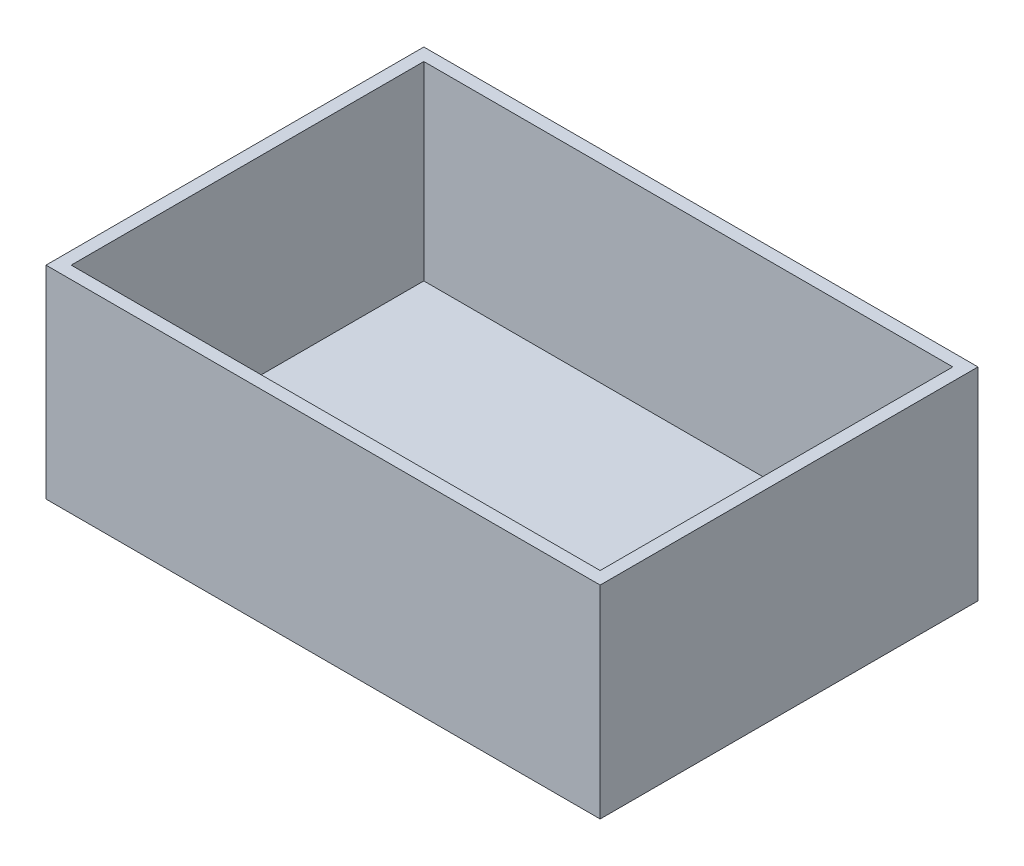
SolidWorks part; units mm, degrees
ref_plane "Front Plane" through (0, 0, 0) normal (0, 0, 1) x (1, 0, 0)
ref_plane "Top Plane" through (0, 0, 0) normal (0, 1, 0) x (1, 0, 0)
ref_plane "Right Plane" through (0, 0, 0) normal (1, 0, 0) x (0, 0, -1)
sketch "Sketch1" plane through (0, 0, 0) normal (0, 1, 0) x (1, 0, 0)
  line L1 (-69.85, -47.625) -> (69.85, -47.625)
  line L2 (-69.85, -47.625) -> (-69.85, 47.625)
  line L3 (-69.85, 47.625) -> (69.85, 47.625)
  line L4 (69.85, -47.625) -> (69.85, 47.625)
  line L5 (-69.85, -47.625) -> (69.85, 47.625) construction
  line L6 (-69.85, 47.625) -> (69.85, -47.625) construction
  point P0 (0, 0)
  dimension "D1" = 95.25
  dimension "D2" = 139.7
extrude "Boss-Extrude1" add sketch "Sketch1" along normal blind 3.175
sketch "Sketch2" plane through (0, 3.175, 0) normal (0, 1, 0) x (1, 0, 0)
  line L8 (66.675, -44.45) -> (66.675, 44.45)
  line L9 (66.675, 44.45) -> (-66.675, 44.45)
  line L10 (-66.675, 44.45) -> (-66.675, -44.45)
  line L11 (-66.675, -44.45) -> (66.675, -44.45)
  line L12 (66.675, -44.45) -> (66.675, 44.45)
  line L13 (66.675, 44.45) -> (-66.675, 44.45)
  line L14 (-66.675, 44.45) -> (-66.675, -44.45)
  line L15 (-66.675, -44.45) -> (66.675, -44.45)
  line L16 (69.85, -47.625) -> (69.85, 47.625)
  line L17 (69.85, 47.625) -> (-69.85, 47.625)
  line L18 (-69.85, 47.625) -> (-69.85, -47.625)
  line L19 (-69.85, -47.625) -> (69.85, -47.625)
  line L20 (69.85, -47.625) -> (69.85, 47.625)
  line L21 (69.85, 47.625) -> (-69.85, 47.625)
  line L22 (-69.85, 47.625) -> (-69.85, -47.625)
  line L23 (-69.85, -47.625) -> (69.85, -47.625)
  dimension "D1" = 3.175
  dimension "D2" = 0
extrude "Boss-Extrude2" add sketch "Sketch2" along normal blind 47.9044
